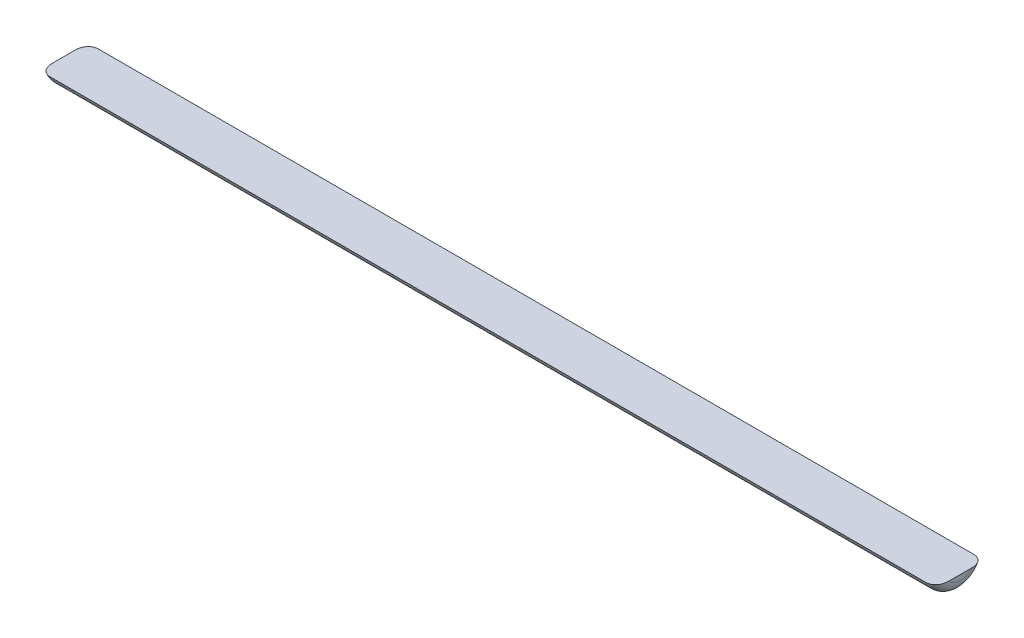
SolidWorks part; units mm, degrees
ref_plane "Front Plane" through (0, 0, 0) normal (0, 0, 1) x (1, 0, 0)
ref_plane "Top Plane" through (0, 0, 0) normal (0, 1, 0) x (1, 0, 0)
ref_plane "Right Plane" through (0, 0, 0) normal (1, 0, 0) x (0, 0, -1)
sketch "Sketch1" plane through (0, 0, 0) normal (1, 0, 0) x (0, 0, -1)
  line L0 (-4.575, -2.0173) -> (4.575, -2.0173)
  arc A0 (-4.575, -2.0173) -> (4.575, -2.0173) centre (0, 0) ccw
  dimension "D1" = 10
  dimension "D3" = 5
  dimension "D2" = 9.15
extrude "Boss-Extrude1" add sketch "Sketch1" along normal blind 170
fillet "Fillet1" radius 2 2 edges at (0, -5, 0) (170, -5, 0)
